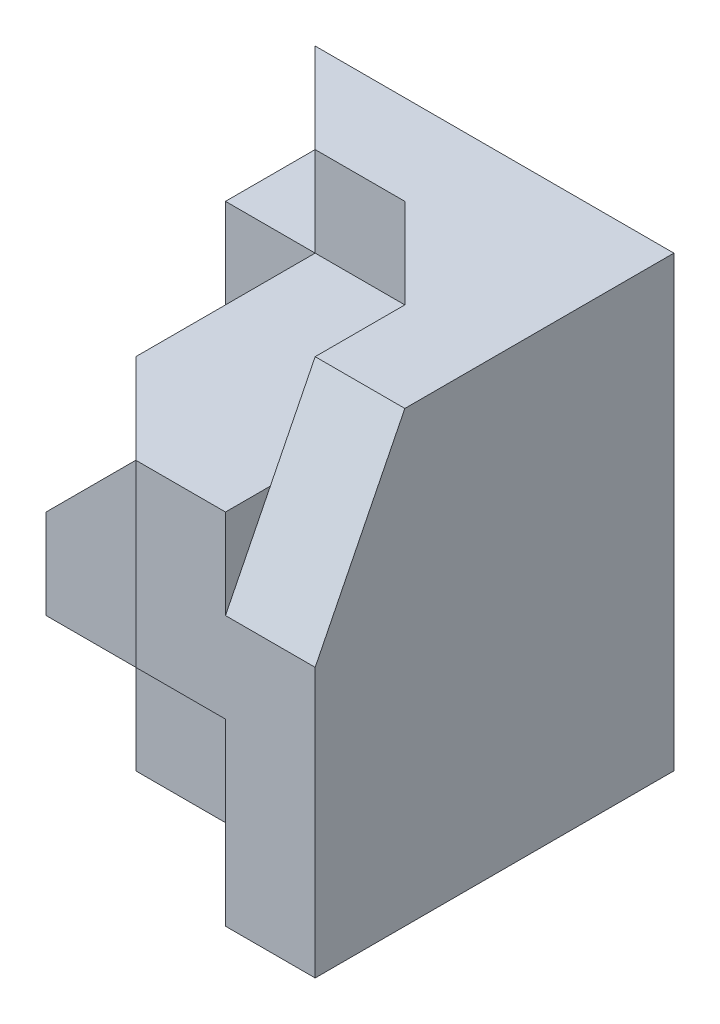
SolidWorks part; units mm, degrees
ref_plane "Front Plane" through (0, 0, 0) normal (0, 0, 1) x (1, 0, 0)
ref_plane "Top Plane" through (0, 0, 0) normal (0, 1, 0) x (1, 0, 0)
ref_plane "Right Plane" through (0, 0, 0) normal (1, 0, 0) x (0, 0, -1)
sketch "Sketch1" plane through (0, 0, 0) normal (0, 1, 0) x (1, 0, 0)
  line L1 (-20, -20) -> (20, -20)
  line L2 (-20, -20) -> (-20, 20)
  line L3 (-20, 20) -> (20, 20)
  line L4 (20, -20) -> (20, 20)
  line L5 (-20, -20) -> (20, 20) construction
  line L6 (-20, 20) -> (20, -20) construction
  point P0 (0, 0)
  dimension "D1" = 40
  dimension "D2" = 40
extrude "Boss-Extrude1" add sketch "Sketch1" along normal blind 50
sketch "Sketch2" plane through (0, 50, 0) normal (0, 1, 0) x (1, 0, 0)
  line L0 (-20, 20) -> (-10, 10)
  line L1 (-10, 10) -> (0, 10)
  line L2 (0, 10) -> (10, 0)
  line L3 (10, 0) -> (10, -20)
  line L4 (-20, -20) -> (20, -20) construction
  line L5 (10, -20) -> (-20, -20)
  line L6 (-20, -20) -> (-20, 20)
  dimension "D1" = 10
  dimension "D2" = 10
  dimension "D3" = 10
  dimension "D4" = 10
  dimension "D5" = 10
extrude "Cut-Extrude1" cut sketch "Sketch2" against normal blind 10
sketch "Sketch3" plane through (20, 0, 0) normal (1, 0, 0) x (0, 0, -1)
  line L0 (-20, 50) -> (-10, 50)
  line L1 (-10, 50) -> (-20, 30)
  line L2 (-20, 50) -> (-20, 0) construction
  line L3 (-20, 30) -> (-20, 50)
  line L4 (-20, 50) -> (20, 50) construction
  dimension "D1" = 10
  dimension "D2" = 20
extrude "Cut-Extrude2" cut sketch "Sketch3" against normal blind 10
sketch "Sketch7" plane through (0, 40, 0) normal (0, 1, 0) x (1, 0, 0)
  line L0 (0, -20) -> (-10, -10)
  line L1 (-20, -20) -> (10, -20) construction
  line L2 (-10, 10) -> (-10, -10)
  line L3 (-10, 10) -> (-20, 10)
  line L4 (-20, 20) -> (-20, -20) construction
  line L5 (-20, 10) -> (-20, -20)
  line L6 (-20, -20) -> (0, -20)
  dimension "D1" = 10
  dimension "D2" = 10
  dimension "D3" = 20
extrude "Cut-Extrude5" cut sketch "Sketch7" against normal blind 10
sketch "Sketch8" plane through (0, 0, 20) normal (0, 0, 1) x (1, 0, 0)
  line L0 (-10, 30) -> (-20, 20)
  line L1 (-20, 30) -> (-20, 0) construction
  line L2 (-20, 20) -> (-20, 30)
  line L3 (-20, 30) -> (-10, 30)
  dimension "D1" = 10
  dimension "D2" = 10
extrude "Cut-Extrude6" cut sketch "Sketch8" against normal blind 30
sketch "Sketch9" plane through (0, 30, 0) normal (0, 1, 0) x (1, 0, 0)
  line L0 (0, -20) -> (-10, -10)
  line L1 (-10, -10) -> (-10, -20)
  line L2 (-10, -20) -> (0, -20)
extrude "Cut-Extrude7" cut sketch "Sketch9" against normal blind 10
sketch "Sketch10" plane through (-10, 0, 0) normal (1, 0, 0) x (0, 0, -1)
  line L1 (-10, 20) -> (-20, 20)
  line L2 (-10, 20) -> (-10, 30)
  line L3 (-10, 30) -> (-20, 30)
  line L4 (-20, 20) -> (-20, 30)
extrude "Cut-Extrude8" cut sketch "Sketch10" against normal blind 10
sketch "Sketch11" plane through (0, 0, 20) normal (0, 0, 1) x (1, 0, 0)
  line L0 (-20, 0) -> (20, 0) construction
  line L1 (10, 0) -> (-20, 0)
  line L2 (10, 0) -> (10, 20)
  line L3 (10, 20) -> (-20, 20)
  line L4 (-20, 0) -> (-20, 20)
  dimension "D1" = 20
  dimension "D2" = 30
extrude "Cut-Extrude9" cut sketch "Sketch11" against normal blind 10
sketch "Sketch13" plane through (0, 0, 10) normal (0, 0, 1) x (1, 0, 0)
  line L1 (-20, 0) -> (-10, 0)
  line L2 (-20, 0) -> (-20, 10)
  line L3 (-20, 10) -> (-10, 10)
  line L4 (-10, 0) -> (-10, 10)
  dimension "D1" = 10
  dimension "D2" = 10
extrude "Cut-Extrude10" cut sketch "Sketch13" against normal through all
